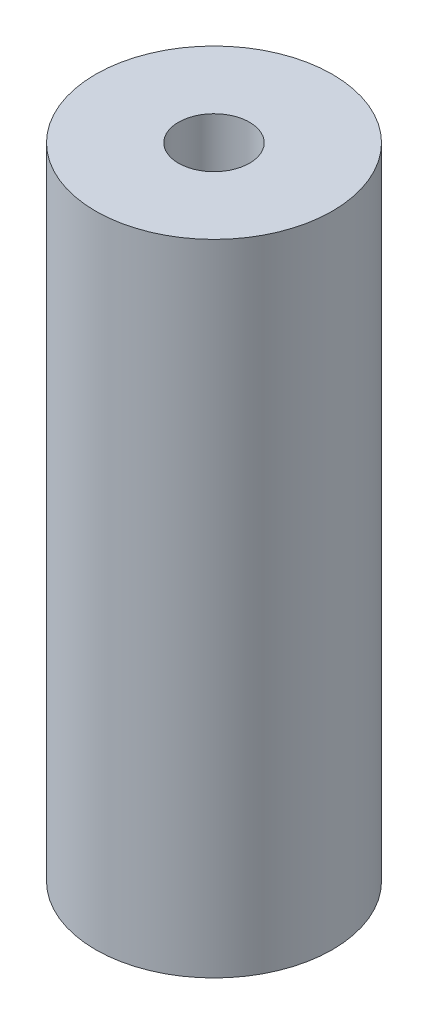
SolidWorks part; units mm, degrees
ref_plane "Alzado" through (0, 0, 0) normal (0, 0, 1) x (1, 0, 0)
ref_plane "Planta" through (0, 0, 0) normal (0, 1, 0) x (1, 0, 0)
ref_plane "Vista lateral" through (0, 0, 0) normal (1, 0, 0) x (0, 0, -1)
sketch "Croquis1" plane through (0, 0, 0) normal (0, 1, 0) x (1, 0, 0)
  circle A0 centre (0, 0) radius 5
  dimension "D1" = 10
extrude "Saliente-Extruir1" add sketch "Croquis1" along normal blind 27
sketch "Croquis2" plane through (0, 27, 0) normal (0, 1, 0) x (1, 0, 0)
  circle A0 centre (0, 0) radius 1.5
  dimension "D1" = 3
extrude "Cortar-Extruir1" cut sketch "Croquis2" against normal blind 5
sketch "Croquis4" plane through (0, 0, 0) normal (0, -1, 0) x (1, 0, 0)
  circle A0 centre (0, 0) radius 1.5
  dimension "D1" = 3
extrude "Cortar-Extruir2" cut sketch "Croquis4" against normal blind 5
